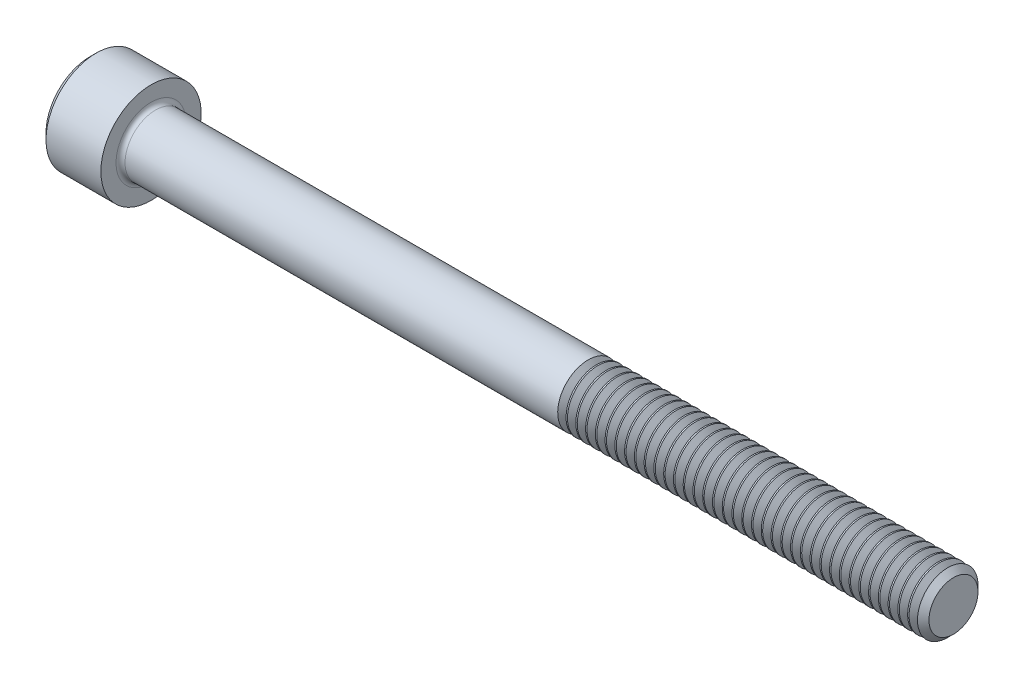
SolidWorks part; units mm, degrees
material "Plain Carbon Steel"
ref_plane "Plane1" through (0, 0, 0) normal (0, 0, 1) x (1, 0, 0)
ref_plane "Plane2" through (0, 0, 0) normal (0, 1, 0) x (1, 0, 0)
ref_plane "Plane3" through (0, 0, 0) normal (1, 0, 0) x (0, 0, -1)
sketch "BodySke" plane through (0, 0, 0) normal (0, 0, 1) x (1, 0, 0)
  line L0 (0, 0) -> (0, 3.4862)
  line L1 (0.4826, 3.9688) -> (4.826, 3.9688)
  line L2 (4.826, 3.9688) -> (4.826, 2.413)
  line L3 (4.826, 2.413) -> (67.8536, 2.413)
  line L4 (68.326, 1.9406) -> (68.326, 0)
  line L5 (68.326, 0) -> (0, 0)
  line L6 (-31.75, 0) -> (127, 0) construction
  line L7 (0, 3.4862) -> (0.4826, 3.9688)
  line L8 (68.326, 1.9406) -> (67.8536, 2.413)
  line L9 (0, -3.4862) -> (0.4826, -3.9688) construction
  line L10 (68.326, -1.9406) -> (67.8536, -2.413) construction
  line L11 (5.6185, 9.525) -> (5.6185, 3.175) construction
  line L12 (39.751, 9.525) -> (39.751, 3.175) construction
  line L13 (30.226, 9.525) -> (30.226, 3.175) construction
  dimension "Diameter" = 4.826
  dimension "Head_ht" = 4.826
  dimension "Length" = 63.5
  dimension "Body_ch_ang" = 45
  dimension "Head_dia" = 7.9375
  dimension "Head_ch_ang" = 45
  dimension "Head_side_ht" = 4.3434
  dimension "Minor_dia" = 3.8811
  dimension "Advance" = 0.7925
  dimension "Thread_nom" = 28.575
  dimension "Thread_length" = 38.1
revolve "Base-Revolve" add sketch "BodySke"
cosmetic thread "ThreadCosmetic" [suppressed]
fillet "Fillet1" radius 0.3556 1 edges at (4.826, 0, 2.413)
sketch "Sketch2" plane through (0, 0, 0) normal (0, 0, 1) x (1, 0, 0)
  line L0 (0, 1.985) -> (2.286, 1.985)
  line L1 (2.286, 1.985) -> (3.432, 0)
  line L2 (-31.75, 0) -> (127, 0) construction
  line L3 (3.432, 0) -> (0, 0)
  line L4 (0, 0) -> (0, 1.985)
  line L5 (0, 3.4862) -> (0, -3.4862) construction
  line L6 (0, 0) -> (47.625, 0) construction
  line L7 (4.826, -3.9688) -> (4.826, 3.9688) construction
  dimension "D1" = 1.985
  dimension "D2" = 60
  dimension "Wall_thickness" = 2.54
revolve "Hex-PreBroach" cut sketch "Sketch2" angle 360 about L6
sketch "Sketch3" plane through (0, 0, 0) normal (-1, 0, 0) x (0, 0.5, 0.866)
  line L0 (1.146, 1.985) -> (-1.146, 1.985)
  line L1 (-1.146, 1.985) -> (-2.2921, 0)
  line L2 (1.146, 1.985) -> (2.2921, 0)
  line L3 (1.146, -1.985) -> (2.2921, 0)
  line L4 (1.146, -1.985) -> (-1.146, -1.985)
  line L5 (-1.146, -1.985) -> (-2.2921, 0)
  dimension "D1" = 1.985
  dimension "D2" = 1.985
  dimension "Hex_size" = 3.97
extrude "Hex" cut sketch "Sketch3" against normal blind 2.286
sketch "Sketch4" plane through (0, 0, 0) normal (-1, 0, 0) x (0, 0, 1)
  line L0 (0, 0) -> (2.3876, 0)
  line L1 (0, 0) -> (6.1484, 3.5498) construction
  line L2 (0, 0) -> (1.1938, 2.0677)
  line L3 (1.9883, 0.576) -> (2.2704, 0.7389)
  line L4 (1.493, 1.4339) -> (1.7751, 1.5968)
  arc A0 (1.9883, 0.576) -> (1.493, 1.4339) centre (0, 0) ccw
  arc A1 (2.3876, 0) -> (2.2704, 0.7389) centre (0, 0) ccw
  arc A2 (1.1938, 2.0677) -> (1.7751, 1.5968) centre (0, 0) cw
  dimension "D1" = 30
  dimension "Spline_n_dim" = 4.1402
  dimension "Spline_m_dim" = 4.7752
  dimension "D2" = 60
  dimension "D3" = 0.4953
  dimension "Spline_p_dim" = 0.9906
extrude "Spline" [suppressed] cut sketch "Sketch4" against normal blind 2.286
pattern_circular "CirPattern1" [suppressed] count 6 every 60
sketch "Sketch5" plane through (0, 0, 0) normal (0, 0, 1) x (1, 0, 0)
  line L0 (-31.75, 0) -> (127, 0) construction
  line L2 (0, 3.4862) -> (0, -3.4862) construction
  circle A0 centre (1.651, 0) radius 0.5905
  dimension "Drilled_hole_dia" = 1.1811
  dimension "Drilled_hole_loc" = 1.651
extrude "Hole" [suppressed] cut sketch "Sketch5" against normal through all and the other way through all
pattern_circular "Drilled-4" [suppressed] count 2 every 60
pattern_circular "Drilled-6" [suppressed] count 3 every 60
sketch "ThdSchSke" plane through (0, 0, 0) normal (0, 0, 1) x (1, 0, 0)
  line L0 (39.751, -1.9406) -> (39.4202, -2.413)
  line L1 (39.751, -1.9406) -> (40.0818, -2.413)
  line L2 (40.0818, -2.413) -> (40.0818, -3.0162)
  line L3 (-3.175, 0) -> (5.1513, 0) construction
  line L5 (40.0818, -3.0162) -> (39.4202, -3.0162)
  line L6 (39.4202, -3.0162) -> (39.4202, -2.413)
  line L7 (0, 3.4862) -> (0, -3.4862) construction
  dimension "Thread_minor" = 3.8811
  dimension "Diameter" = 4.826
  dimension "Start" = 39.751
  dimension "SideAngle" = 55
  dimension "VeeAngle" = 70
  dimension "Overcut" = 6.0325
revolve "ThreadSchematic" cut sketch "ThdSchSke" angle 360 about L3
pattern_linear "ThdSchPat" count 37 spacing 0.7723 along (1, 0, 0) of "ThreadSchematic"
equation "\"D2@Sketch3\" = \"Hex_size@Sketch3\" / 2"
equation "\"D1@Sketch3\" = \"Hex_size@Sketch3\" / 2"
equation "\"D1@Sketch2\" = \"Hex_size@Sketch3\" / 2"
equation "\"D3@Sketch4\" = \"Spline_p_dim@Sketch4\" / 2"
equation "\"Thread_minor@ThreadCosmetic\"  =  \"Minor_dia@BodySke\""
equation "\"D2@CirPattern1\" = 360 / \"Num_teeth@CirPattern1\""
equation "\"Wall_thickness@Sketch2\" = \"Head_ht@BodySke\" - \"Key_eng@Hex\""
equation "\"Thread_length@ThreadCosmetic\" = ((sgn( (\"Length@BodySke\" - \"Advance@BodySke\" ) - \"Thread_nom@BodySke\" )-1)*( (\"Length@BodySke\" - \"Advance@BodySke\" ) - \"Thread_nom@BodySke\" ))/-2+ \"Thread_nom@BodySke\""
equation "\"Thread_minor@ThdSchSke\" = \"Minor_dia@BodySke\""
equation "\"Diameter@ThdSchSke\" = \"Diameter@BodySke\""
equation "\"Overcut@ThdSchSke\" = \"Diameter@BodySke\" * 1.25"
equation "\"Start@ThdSchSke\" = \"Head_ht@BodySke\" + \"Length@BodySke\" - \"Thread_length@ThreadCosmetic\"  '---Non-countersunk---"
equation "\"Num_threads@ThdSchPat\" = int( \"Thread_length@ThreadCosmetic\" / \"Advance@BodySke\" + 0.999 )  + 1"
equation "\"Advance@ThdSchPat\" = \"Thread_length@ThreadCosmetic\" /  (\"Num_threads@ThdSchPat\" - 1) 'relax it"
equation "\"Num_threads@ThdSchPat\" = \"Num_threads@ThdSchPat\" - sgn( \"Num_threads@ThdSchPat\" - 1) '---chamfered tips only---"
